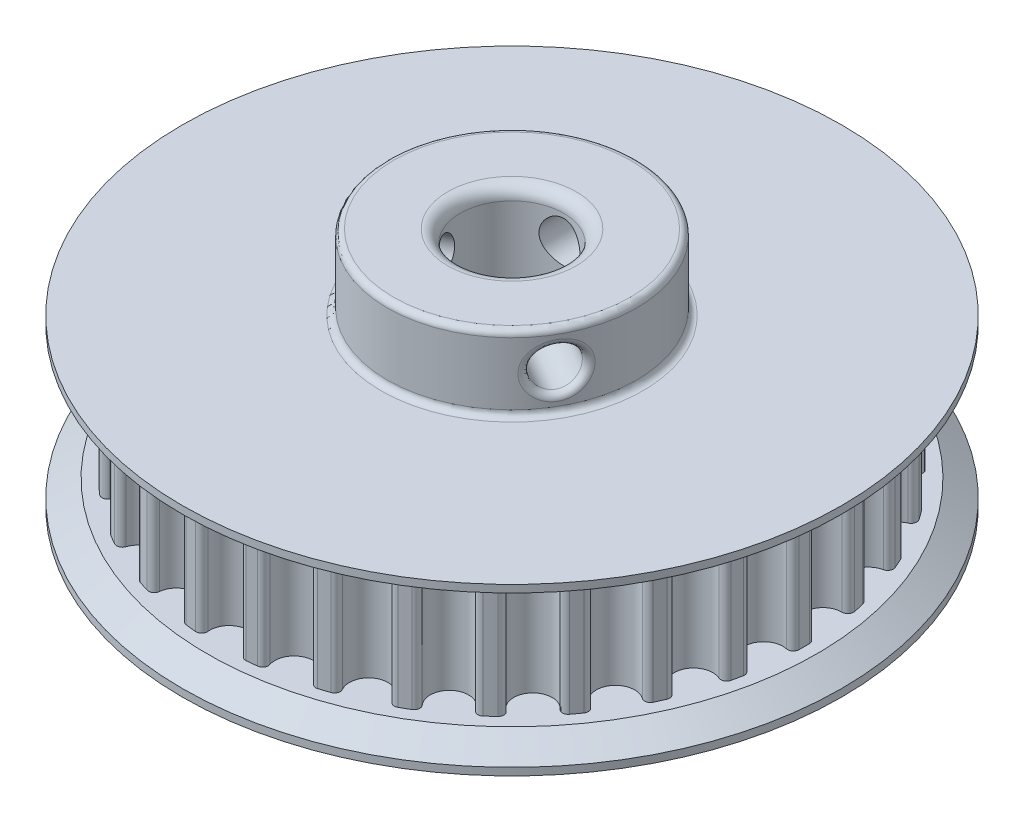
SolidWorks part; units mm, degrees
ref_plane "Plan de face" through (0, 0, 0) normal (0, 0, 1) x (1, 0, 0)
ref_plane "Plan de dessus" through (0, 0, 0) normal (0, 1, 0) x (1, 0, 0)
ref_plane "Plan de droite" through (0, 0, 0) normal (1, 0, 0) x (0, 0, -1)
sketch "Esquisse1" plane through (0, 0, 0) normal (0, 1, 0) x (1, 0, 0)
  line L0 (0, 0) -> (-2.449, 23.3007)
  line L2 (2.449, 23.3007) -> (0, 0)
  line L3 (0, 23.429) -> (0, 0) construction
  line L4 (-2.449, 23.3007) -> (2.449, 23.3007) construction
  circle A1 centre (0, 0) radius 23.429 construction
  arc A2 (-1.5343, 22.836) -> (1.5343, 22.836) centre (0, 22.672) ccw
  arc A3 (-2.449, 23.3007) -> (-2.0293, 23.341) centre (0, 0) cw
  arc A4 (-2.0293, 23.341) -> (-1.5343, 22.836) centre (-1.9897, 22.8847) cw
  arc A5 (2.449, 23.3007) -> (2.0293, 23.341) centre (0, 0) ccw
  arc A6 (2.0293, 23.341) -> (1.5343, 22.836) centre (1.9897, 22.8847) ccw
  arc A7 (-1.5343, 22.836) -> (-1.3662, 23.3892) centre (0, 22.672) cw construction
  arc A8 (1.5343, 22.836) -> (1.3662, 23.3892) centre (0, 22.672) ccw construction
  point P6 (0, 21.129)
  dimension "D2" = 1.543
  dimension "D3" = 0.458
  dimension "D1" = 4.898
  dimension "D4" = 2.3
  dimension "D5" = 12
extrude "Boss.-Extru.1" add sketch "Esquisse1" along normal blind 9.3
pattern_circular "Répétition circulaire1" count 30 over 360 about axis through (0, 0, 0) along (0, 1, 0) of "Boss.-Extru.1"
ref_plane "Plan1" through (0, 4.65, 0) normal (0, -1, 0) x (-1, 0, 0)
sketch "Esquisse2" plane through (0, 9.3, 0) normal (0, 1, 0) x (1, 0, 0)
  circle A0 centre (0, 0) radius 26.429
  arc A1 (22.8257, -5.2827) -> (23.001, -4.458) centre (0, 0) ccw construction
  dimension "D1" = 3
extrude "Boss.-Extru.2" add sketch "Esquisse2" along normal blind 2
mirror "Symétrie1" about plane through (0, 4.65, 0) normal (0, -1, 0) of "Boss.-Extru.2"
chamfer "Chanfrein1" distance 2 angle 35 2 edges at (0, 9.3, 26.429) (0, 0, 26.429)
sketch "Esquisse4" plane through (0, 11.3, 0) normal (0, 1, 0) x (1, 0, 0)
  circle A0 centre (0, 0) radius 10
  dimension "D1" = 20
extrude "Boss.-Extru.3" add sketch "Esquisse4" along normal blind 6
sketch "Esquisse5" plane through (0, 0, 0) normal (0, 0, 1) x (1, 0, 0)
  line L0 (0, 0) -> (0, 14.3) construction
  line L1 (10, 17.3) -> (-10, 17.3) construction
  circle A0 centre (0, 14.3) radius 1.65
  dimension "D2" = 3.3
  dimension "D1" = 3
extrude "Enlèv. mat.-Extru.2" cut sketch "Esquisse5" against normal through all
pattern_circular "Répétition circulaire2" count 3 over 360 about axis through (0, 17.3, 0) along (0, -1, 0) of "Enlèv. mat.-Extru.2"
sketch "Esquisse3" plane through (0, 17.3, 0) normal (0, 1, 0) x (1, 0, 0)
  circle A0 centre (0, 0) radius 4.15
  dimension "D1" = 8.3
extrude "Enlèv. mat.-Extru.1" cut sketch "Esquisse3" against normal up to next
fillet "Congé1" radius 1 2 edges at (0, -2, -4.15) (0, 17.3, 4.15)
fillet "Congé2" radius 0.5 5 edges at (0, 11.3, 10) (0, 17.3, 10) (0.3544, 12.6885, -9.9937) (-7.7413, 13.9455, 6.3302) (9.3528, 13.9455, 3.5391)
equation "\"nb_tooth\"= 30"
equation "\"D5@Esquisse1\"=360/\"nb_tooth\""
equation "\"D1@Répétition circulaire1\"=\"nb_tooth\""
